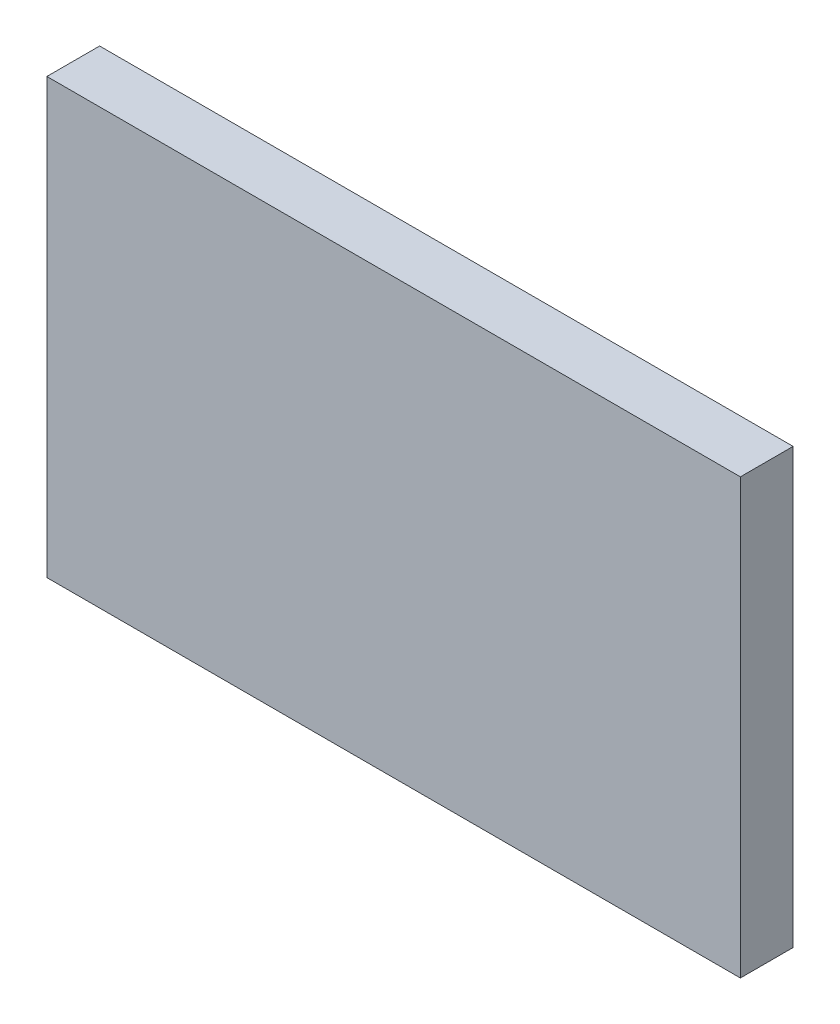
SolidWorks part; units mm, degrees
ref_plane "Face" through (0, 0, 0) normal (0, 0, 1) x (1, 0, 0)
ref_plane "Dessus" through (0, 0, 0) normal (0, 1, 0) x (1, 0, 0)
ref_plane "Droite" through (0, 0, 0) normal (1, 0, 0) x (0, 0, -1)
sketch "Sketch1" plane through (0, 0, 0) normal (0, 1, 0) x (1, 0, 0)
  line L1 (32.875, -2.5) -> (-32.875, -2.5)
  line L2 (32.875, -2.5) -> (32.875, 2.5)
  line L3 (32.875, 2.5) -> (-32.875, 2.5)
  line L4 (-32.875, -2.5) -> (-32.875, 2.5)
  line L5 (32.875, -2.5) -> (-32.875, 2.5) construction
  line L6 (32.875, 2.5) -> (-32.875, -2.5) construction
  point P0 (0, 0)
  dimension "D1" = 65.75
  dimension "D2" = 5
extrude "Boss-Extrude1" add sketch "Sketch1" along normal blind 41.15
